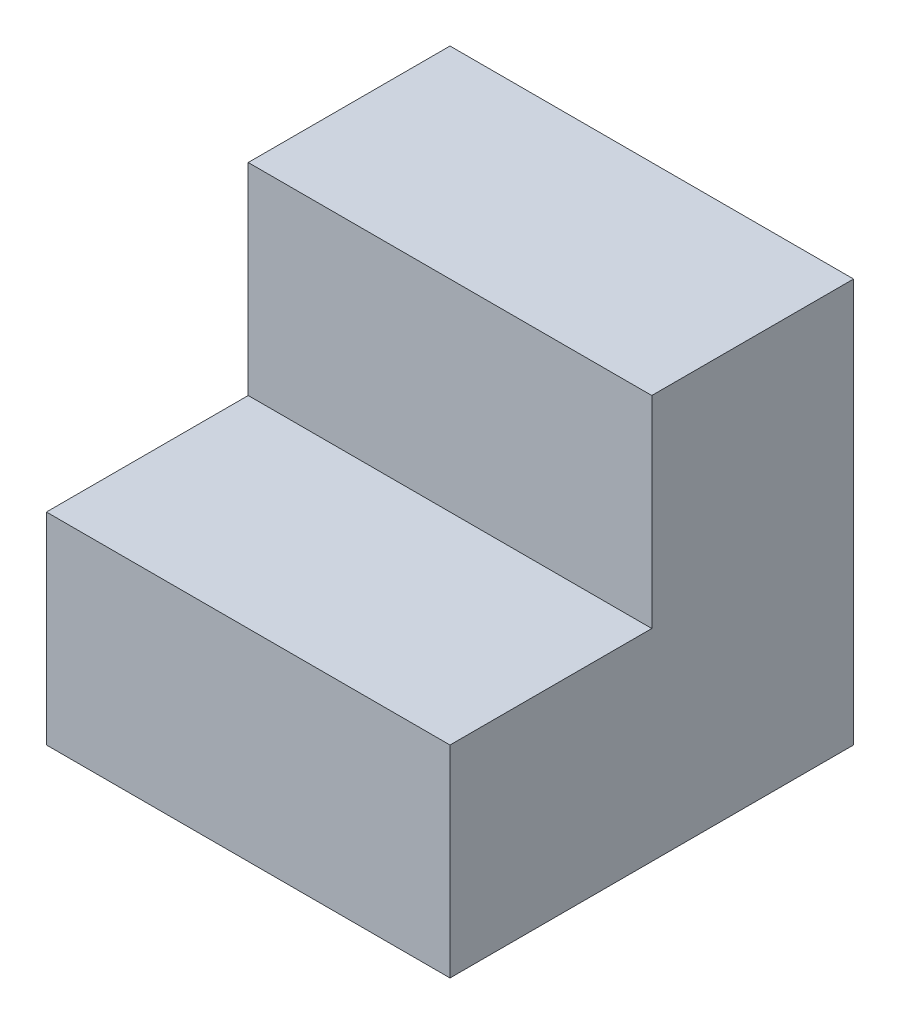
SolidWorks part; units mm, degrees
material "Plain Carbon Steel"
ref_plane "Front Plane" through (0, 0, 0) normal (0, 0, 1) x (1, 0, 0)
ref_plane "Top Plane" through (0, 0, 0) normal (0, 1, 0) x (1, 0, 0)
ref_plane "Right Plane" through (0, 0, 0) normal (1, 0, 0) x (0, 0, -1)
sketch "Sketch1" plane through (0, 0, 0) normal (1, 0, 0) x (0, 0, -1)
  line L0 (-30, 15) -> (-15, 15)
  line L1 (0, 0) -> (-30, 0)
  line L2 (0, 0) -> (0, 30)
  line L3 (0, 30) -> (-15, 30)
  line L4 (-30, 0) -> (-30, 15)
  line L5 (-15, 15) -> (-15, 30)
  dimension "D1" = 30
  dimension "D2" = 15
  dimension "D3" = 15
extrude "Boss-Extrude1" add sketch "Sketch1" along normal mid plane 30
